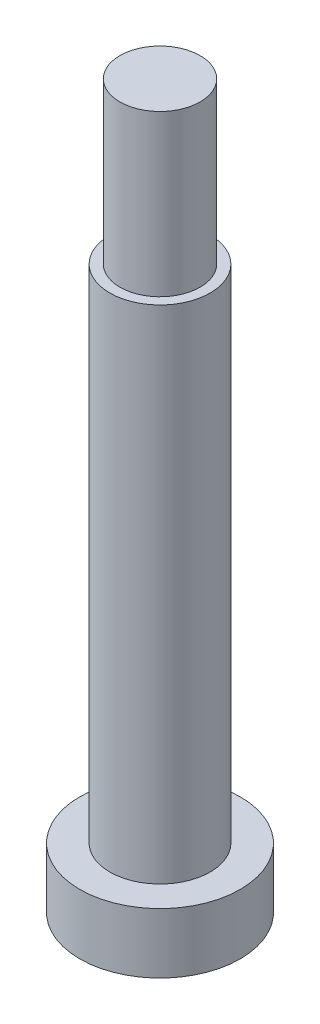
SolidWorks part; units mm, degrees
material "1060 合金"
ref_plane "前视基准面" through (0, 0, 0) normal (0, 0, 1) x (1, 0, 0)
ref_plane "上视基准面" through (0, 0, 0) normal (0, 1, 0) x (1, 0, 0)
ref_plane "右视基准面" through (0, 0, 0) normal (1, 0, 0) x (0, 0, -1)
sketch "草图1" plane through (0, 0, 0) normal (0, 1, 0) x (1, 0, 0)
  circle A0 centre (0, 0) radius 2.5
  dimension "D1" = 5
extrude "凸台-拉伸1" add sketch "草图1" along normal blind 25
sketch "草图2" plane through (0, 25, 0) normal (0, 1, 0) x (1, 0, 0)
  circle A0 centre (0, 0) radius 2
  dimension "D1" = 4
extrude "凸台-拉伸2" add sketch "草图2" along normal blind 8
cosmetic thread "装饰螺纹线1" parameters "D2"=3.242
sketch "草图3" plane through (0, 0, 0) normal (0, -1, 0) x (1, 0, 0)
  circle A0 centre (0, 0) radius 4
  dimension "D1" = 8
extrude "凸台-拉伸3" add sketch "草图3" along normal blind 3
